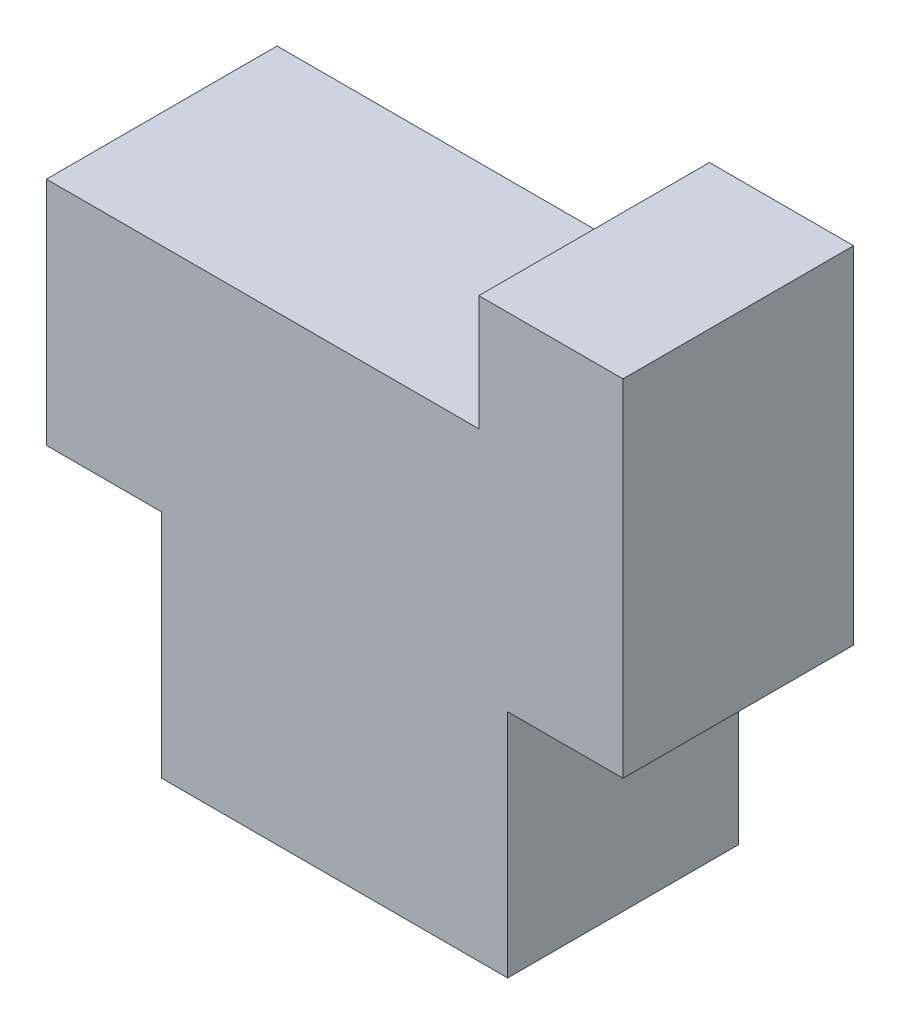
SolidWorks part; units mm, degrees
ref_plane "Front Plane" through (0, 0, 0) normal (0, 0, 1) x (1, 0, 0)
ref_plane "Top Plane" through (0, 0, 0) normal (0, 1, 0) x (1, 0, 0)
ref_plane "Right Plane" through (0, 0, 0) normal (1, 0, 0) x (0, 0, -1)
sketch "Sketch1" plane through (0, 0, 0) normal (0, 0, 1) x (1, 0, 0)
  line L0 (0, 0) -> (6, 0)
  line L1 (0, 0) -> (0, 4)
  line L2 (6, 0) -> (6, 4)
  line L3 (6, 4) -> (8, 4)
  line L4 (-2, 8) -> (5.5, 8)
  line L5 (5.5, 8) -> (5.5, 10)
  line L6 (5.5, 10) -> (8, 10)
  line L7 (8, 10) -> (8, 4)
  line L8 (0, 4) -> (-2, 4)
  line L9 (-2, 4) -> (-2, 8)
  dimension "D1" = 6
  dimension "D2" = 8
extrude "Boss-Extrude1" add sketch "Sketch1" along normal blind 4
